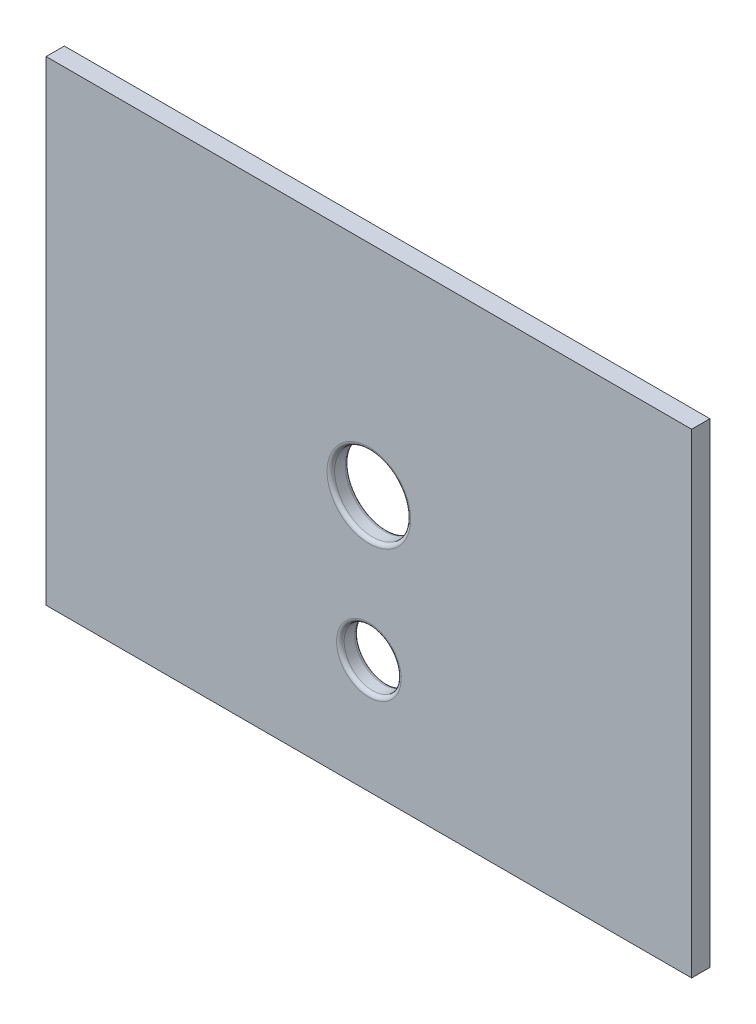
SolidWorks part; units mm, degrees
ref_plane "Ebene vorne" through (0, 0, 0) normal (0, 0, 1) x (1, 0, 0)
ref_plane "Ebene oben" through (0, 0, 0) normal (0, 1, 0) x (1, 0, 0)
ref_plane "Ebene rechts" through (0, 0, 0) normal (1, 0, 0) x (0, 0, -1)
sketch "Sketch1" plane through (0, 0, 0) normal (0, 0, 1) x (1, 0, 0)
  line L0 (0, -62.5) -> (0, 62.5) construction
  line L1 (-84.9, 62.5) -> (84.9, 62.5)
  line L2 (-84.9, 62.5) -> (-84.9, -62.5)
  line L3 (-84.9, -62.5) -> (84.9, -62.5)
  line L4 (84.9, 62.5) -> (84.9, -62.5)
  line L5 (-84.9, 62.5) -> (84.9, -62.5) construction
  line L6 (-84.9, -62.5) -> (84.9, 62.5) construction
  circle A0 centre (0, 5) radius 10
  point P0 (0, 0)
  dimension "D3" = 20
  dimension "D4" = 67.5
  dimension "D1" = 169.8
  dimension "D2" = 125
extrude "Boss-Extrude1" add sketch "Sketch1" along normal blind 4.8
sketch "Sketch2" plane through (0, 0, 4.8) normal (0, 0, 1) x (1, 0, 0)
  line L0 (0, 62.5) -> (0, -62.5) construction
  line L1 (84.9, 62.5) -> (-84.9, 62.5) construction
  line L2 (-84.9, -62.5) -> (84.9, -62.5) construction
  circle A1 centre (0, -32.5) radius 7.5
  point P8 (0, -29.7757)
  dimension "D1" = 15
  dimension "D2" = 30
extrude "Cut-Extrude1" cut sketch "Sketch2" against normal through all
fillet "Fillet1" radius 1 4 edges at (7.5, -32.5, 0) (10, 5, 0) (10, 5, 4.8) (7.5, -32.5, 4.8)
